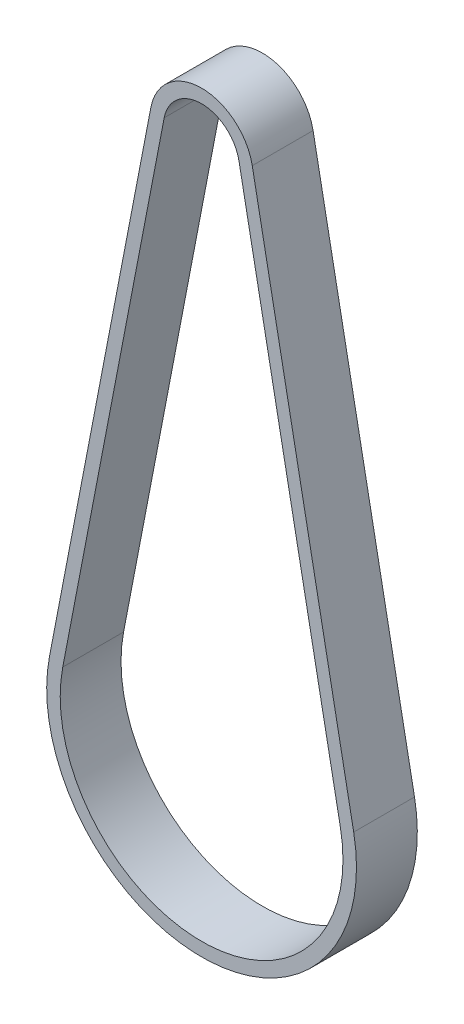
SolidWorks part; units mm, degrees
material "Rubber"
ref_plane "Front Plane" through (0, 0, 0) normal (0, 0, 1) x (1, 0, 0)
ref_plane "Top Plane" through (0, 0, 0) normal (0, 1, 0) x (1, 0, 0)
ref_plane "Right Plane" through (0, 0, 0) normal (1, 0, 0) x (0, 0, -1)
sketch "Sketch1" plane through (0, 0, 0) normal (0, 0, 1) x (1, 0, 0)
  line L0 (-7.4971, 1.4445) -> (-22.5061, -76.4537)
  line L1 (7.4971, 1.4445) -> (22.5061, -76.4537)
  arc A0 (7.4971, 1.4445) -> (-7.4971, 1.4445) centre (0, 0) ccw
  arc A1 (-22.5061, -76.4537) -> (22.5061, -76.4537) centre (0, -80.79) ccw
  dimension "D1" = 7.635
  dimension "D2" = 22.92
  dimension "D3" = 80.79
extrude "Extrude-Thin1" add sketch "Sketch1" along normal mid plane 9 thin thin type one direction reverse wall 2
